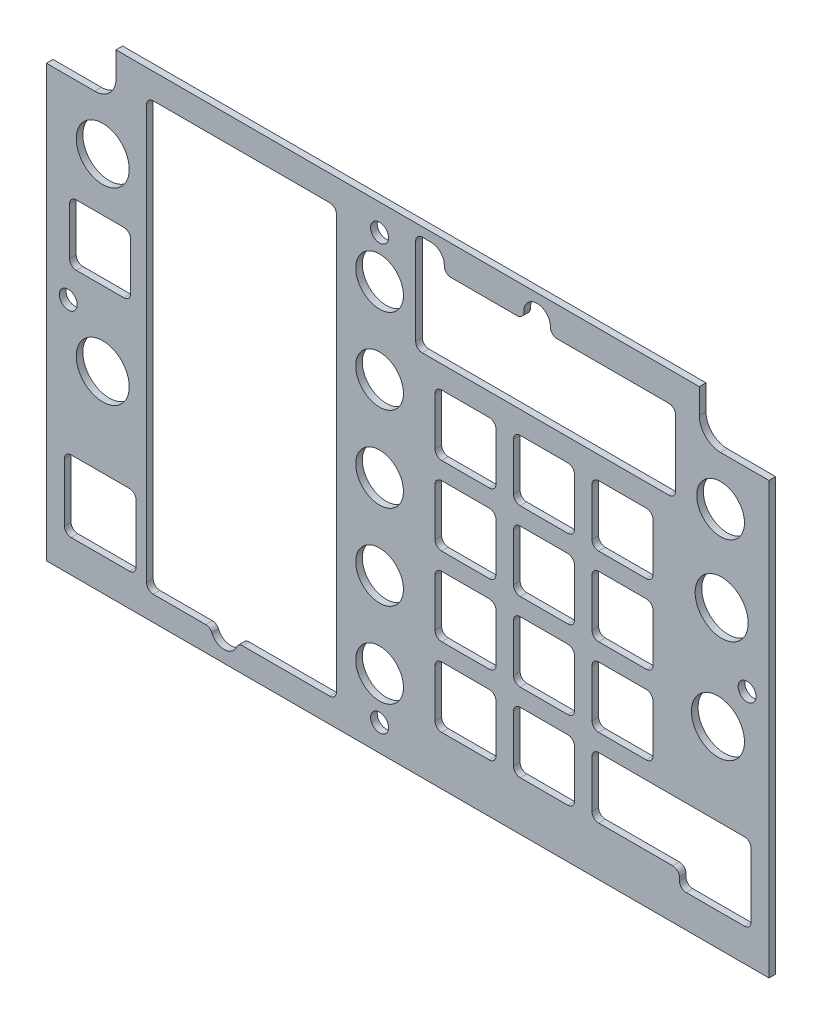
SolidWorks part; units mm, degrees
material "ABS PC"
ref_plane "Front Plane" through (0, 0, 0) normal (0, 0, 1) x (1, 0, 0)
ref_plane "Top Plane" through (0, 0, 0) normal (0, 1, 0) x (1, 0, 0)
ref_plane "Right Plane" through (0, 0, 0) normal (1, 0, 0) x (0, 0, -1)
sketch "Sketch1" plane through (0, 0, 0) normal (0, 0, 1) x (1, 0, 0)
  line L8 (58.2068, 169.534) -> (58.2068, 175.5665)
  line L9 (58.2068, 175.5665) -> (-81.4932, 175.5665)
  line L10 (-81.4932, 175.5665) -> (-81.4932, 169.534)
  line L11 (-86.5732, 164.454) -> (-98.162, 164.454)
  line L12 (-98.162, 164.454) -> (-98.162, 61.2665)
  line L13 (-98.162, 61.2665) -> (74.8755, 61.2665)
  line L14 (74.8755, 61.2665) -> (74.8755, 164.454)
  line L15 (74.8755, 164.454) -> (63.2868, 164.454)
  line L16 (58.2068, 169.534) -> (58.2068, 175.5665)
  line L17 (58.2068, 175.5665) -> (-81.4932, 175.5665)
  line L18 (-81.4932, 175.5665) -> (-81.4932, 169.534)
  line L19 (-86.5732, 164.454) -> (-98.162, 164.454)
  line L20 (-98.162, 164.454) -> (-98.162, 61.2665)
  line L21 (-98.162, 61.2665) -> (74.8755, 61.2665)
  line L22 (74.8755, 61.2665) -> (74.8755, 164.454)
  line L23 (74.8755, 164.454) -> (63.2868, 164.454)
  arc A2 (58.2068, 169.534) -> (63.2868, 164.454) centre (63.2868, 169.534) ccw
  arc A3 (-86.5732, 164.454) -> (-81.4932, 169.534) centre (-86.5732, 169.534) ccw
  arc A4 (58.2068, 169.534) -> (63.2868, 164.454) centre (63.2868, 169.534) ccw
  arc A5 (-86.5732, 164.454) -> (-81.4932, 169.534) centre (-86.5732, 169.534) ccw
  dimension "D1" = 0
extrude "Boss-Extrude1" add sketch "Sketch1" along normal blind 1.5875
sketch "Sketch2" plane through (0, 0, 1.5875) normal (0, 0, 1) x (1, 0, 0)
  line L0 (32.4893, 129.402) -> (47.0943, 129.402)
  line L1 (32.4893, 144.007) -> (32.4893, 129.402)
  line L2 (47.0943, 144.007) -> (32.4893, 144.007)
  line L3 (47.0943, 129.402) -> (47.0943, 144.007)
  line L4 (69.005, 84.6495) -> (55.005, 70.6495) construction
  line L5 (-78.2558, 84.633) -> (-92.2558, 70.633) construction
  line L6 (70.5775, 69.077) -> (53.4325, 69.077)
  line L7 (70.5775, 69.077) -> (70.5775, 86.222)
  line L8 (70.5775, 86.222) -> (53.4325, 86.222)
  line L9 (53.4325, 69.077) -> (53.4325, 86.222)
  line L10 (70.5775, 69.077) -> (53.4325, 86.222) construction
  line L11 (70.5775, 86.222) -> (53.4325, 69.077) construction
  line L12 (13.6933, 129.402) -> (28.2983, 129.402)
  line L13 (13.6933, 144.007) -> (13.6933, 129.402)
  line L14 (28.2983, 144.007) -> (13.6933, 144.007)
  line L15 (28.2983, 129.402) -> (28.2983, 144.007)
  line L16 (9.5023, 144.007) -> (-5.1027, 144.007)
  line L17 (9.5023, 129.402) -> (9.5023, 144.007)
  line L18 (-5.1027, 129.402) -> (9.5023, 129.402)
  line L19 (-5.1027, 144.007) -> (-5.1027, 129.402)
  line L20 (32.4893, 110.606) -> (32.4893, 129.402) construction
  line L22 (49.8768, 158.9295) -> (-7.1232, 158.9295) construction
  line L23 (52.4918, 168.4545) -> (-9.7382, 168.4545)
  line L24 (52.4918, 168.4545) -> (52.4918, 149.4045)
  line L25 (52.4918, 149.4045) -> (-9.7382, 149.4045)
  line L26 (32.4893, 73.014) -> (47.0943, 73.014)
  line L27 (32.4893, 87.619) -> (32.4893, 73.014)
  line L28 (47.0943, 87.619) -> (32.4893, 87.619)
  line L29 (47.0943, 73.014) -> (47.0943, 87.619)
  line L30 (32.4893, 73.014) -> (47.0943, 73.014)
  line L31 (32.4893, 87.619) -> (32.4893, 73.014)
  line L32 (47.0943, 87.619) -> (32.4893, 87.619)
  line L33 (47.0943, 73.014) -> (47.0943, 87.619)
  line L34 (32.4893, 91.81) -> (47.0943, 91.81)
  line L35 (32.4893, 106.415) -> (32.4893, 91.81)
  line L36 (47.0943, 106.415) -> (32.4893, 106.415)
  line L37 (47.0943, 91.81) -> (47.0943, 106.415)
  line L38 (32.4893, 91.81) -> (47.0943, 91.81)
  line L39 (32.4893, 106.415) -> (32.4893, 91.81)
  line L40 (47.0943, 106.415) -> (32.4893, 106.415)
  line L41 (47.0943, 91.81) -> (47.0943, 106.415)
  line L42 (32.4893, 110.606) -> (47.0943, 110.606)
  line L43 (32.4893, 125.211) -> (32.4893, 110.606)
  line L44 (47.0943, 125.211) -> (32.4893, 125.211)
  line L45 (47.0943, 110.606) -> (47.0943, 125.211)
  line L46 (32.4893, 110.606) -> (47.0943, 110.606)
  line L47 (32.4893, 125.211) -> (32.4893, 110.606)
  line L48 (47.0943, 125.211) -> (32.4893, 125.211)
  line L49 (47.0943, 110.606) -> (47.0943, 125.211)
  line L50 (-9.7382, 168.4545) -> (-9.7382, 149.4045)
  line L51 (13.6933, 73.014) -> (28.2983, 73.014)
  line L52 (13.6933, 87.619) -> (13.6933, 73.014)
  line L53 (28.2983, 87.619) -> (13.6933, 87.619)
  line L54 (28.2983, 73.014) -> (28.2983, 87.619)
  line L55 (13.6933, 73.014) -> (28.2983, 73.014)
  line L56 (13.6933, 87.619) -> (13.6933, 73.014)
  line L57 (28.2983, 87.619) -> (13.6933, 87.619)
  line L58 (28.2983, 73.014) -> (28.2983, 87.619)
  line L59 (13.6933, 91.81) -> (28.2983, 91.81)
  line L60 (13.6933, 106.415) -> (13.6933, 91.81)
  line L61 (28.2983, 106.415) -> (13.6933, 106.415)
  line L62 (-93.8283, 69.0605) -> (-76.6833, 69.0605)
  line L63 (-93.8283, 69.0605) -> (-93.8283, 86.2055)
  line L64 (-93.8283, 86.2055) -> (-76.6833, 86.2055)
  line L65 (-76.6833, 69.0605) -> (-76.6833, 86.2055)
  line L66 (-93.8283, 69.0605) -> (-76.6833, 86.2055) construction
  line L67 (-93.8283, 86.2055) -> (-76.6833, 69.0605) construction
  line L94 (28.2983, 91.81) -> (28.2983, 106.415)
  line L95 (13.6933, 91.81) -> (28.2983, 91.81)
  line L96 (13.6933, 106.415) -> (13.6933, 91.81)
  line L97 (28.2983, 106.415) -> (13.6933, 106.415)
  line L98 (28.2983, 91.81) -> (28.2983, 106.415)
  line L99 (13.6933, 110.606) -> (28.2983, 110.606)
  line L100 (13.6933, 125.211) -> (13.6933, 110.606)
  line L101 (28.2983, 125.211) -> (13.6933, 125.211)
  line L102 (28.2983, 110.606) -> (28.2983, 125.211)
  line L103 (13.6933, 110.606) -> (28.2983, 110.606)
  line L104 (13.6933, 125.211) -> (13.6933, 110.606)
  line L105 (28.2983, 125.211) -> (13.6933, 125.211)
  line L106 (28.2983, 110.606) -> (28.2983, 125.211)
  line L107 (9.5023, 125.211) -> (-5.1027, 125.211)
  line L108 (9.5023, 110.606) -> (9.5023, 125.211)
  line L109 (-5.1027, 110.606) -> (9.5023, 110.606)
  line L110 (-5.1027, 125.211) -> (-5.1027, 110.606)
  line L111 (9.5023, 125.211) -> (-5.1027, 125.211)
  line L112 (9.5023, 110.606) -> (9.5023, 125.211)
  line L113 (-5.1027, 110.606) -> (9.5023, 110.606)
  line L114 (-5.1027, 125.211) -> (-5.1027, 110.606)
  line L115 (-5.1027, 91.81) -> (9.5023, 91.81)
  line L116 (-5.1027, 106.415) -> (-5.1027, 91.81)
  line L117 (9.5023, 106.415) -> (-5.1027, 106.415)
  line L118 (9.5023, 91.81) -> (9.5023, 106.415)
  line L119 (-5.1027, 91.81) -> (9.5023, 91.81)
  line L120 (-5.1027, 106.415) -> (-5.1027, 91.81)
  line L121 (9.5023, 106.415) -> (-5.1027, 106.415)
  line L122 (9.5023, 91.81) -> (9.5023, 106.415)
  line L123 (-5.1027, 73.014) -> (9.5023, 73.014)
  line L124 (-5.1027, 87.619) -> (-5.1027, 73.014)
  line L125 (9.5023, 87.619) -> (-5.1027, 87.619)
  line L126 (9.5023, 73.014) -> (9.5023, 87.619)
  line L127 (-5.1027, 73.014) -> (9.5023, 73.014)
  line L128 (-5.1027, 87.619) -> (-5.1027, 73.014)
  line L129 (9.5023, 87.619) -> (-5.1027, 87.619)
  line L130 (9.5023, 73.014) -> (9.5023, 87.619)
  line L131 (-78.0007, 139.689) -> (-92.6057, 139.689)
  line L132 (-78.0007, 125.084) -> (-78.0007, 139.689)
  line L133 (-92.6057, 125.084) -> (-78.0007, 125.084)
  line L134 (-92.6057, 139.689) -> (-92.6057, 125.084)
  line L135 (-78.0007, 139.689) -> (-92.6057, 139.689)
  line L136 (-78.0007, 125.084) -> (-78.0007, 139.689)
  line L137 (-92.6057, 125.084) -> (-78.0007, 125.084)
  line L138 (-92.6057, 139.689) -> (-92.6057, 125.084)
  line L139 (-74.1732, 67.1295) -> (-28.7112, 67.1295)
  line L140 (-74.1732, 169.4495) -> (-74.1732, 67.1295)
  line L141 (-28.7112, 169.4495) -> (-74.1732, 169.4495)
  line L142 (-28.7112, 67.1295) -> (-28.7112, 169.4495)
  line L143 (-74.1732, 67.1295) -> (-28.7112, 67.1295)
  line L144 (-74.1732, 169.4495) -> (-74.1732, 67.1295)
  line L145 (-28.7112, 169.4495) -> (-74.1732, 169.4495)
  line L146 (-28.7112, 67.1295) -> (-28.7112, 169.4495)
  circle A0 centre (-84.6682, 152.389) radius 6.35
  circle A1 centre (-84.6682, 107.304) radius 6.35
  circle A2 centre (63.5408, 132.3865) radius 6.35
  circle A3 centre (62.6518, 107.304) radius 6.35
  circle A10 centre (-18.3742, 77.7765) radius 5.715 construction
  circle A11 centre (-18.3742, 98.0965) radius 5.715 construction
  circle A12 centre (-18.3742, 118.4165) radius 5.715 construction
  circle A13 centre (-18.3742, 138.7365) radius 5.715 construction
  circle A14 centre (-18.3742, 159.0565) radius 5.715 construction
  circle A15 centre (-18.3742, 77.7765) radius 5.715
  circle A16 centre (-18.3742, 98.0965) radius 5.715
  circle A17 centre (-18.3742, 118.4165) radius 5.715
  circle A18 centre (-18.3742, 138.7365) radius 5.715
  circle A19 centre (-18.3742, 159.0565) radius 5.715
  circle A20 centre (63.2868, 152.7065) radius 5.715 construction
  circle A21 centre (63.2868, 152.7065) radius 5.715
  point P94 (-85.2558, 77.633)
  point P97 (-85.2558, 77.633)
  point P98 (62.005, 77.6495)
  point P99 (62.005, 77.6495)
  point P104 (21.3768, 158.9295)
  point P109 (21.3768, 168.4545)
  point P113 (52.4918, 158.9295)
  dimension "D1" = 12.7
  dimension "D16" = 18.796
  dimension "D17" = 19.05
  dimension "D18" = 62.23
  dimension "D2" = 17.145
  dimension "D3" = 0
  dimension "D4" = 0
  dimension "D5" = 0
  dimension "D6" = 2
  dimension "D7" = 0
  dimension "D8" = 0
  dimension "D9" = 0
  dimension "D10" = 0
  dimension "D11" = 0
  dimension "D12" = 0
  dimension "D13" = 0
  dimension "D14" = 0
extrude "Cut-Extrude1" cut sketch "Sketch2" against normal through all
hole_wizard "#6 Clearance Hole2" positions "Sketch5" profile "Sketch6" hole size "#6" standard "ANSI Inch" end condition through all
sketch "Sketch5" plane through (-11.6432, -6.6627, -3.175) normal (0, 0, -1) x (-1, 0, 0)
  point P0 (-81.28, 124.6982)
  point P3 (6.731, 175.8792)
  point P6 (81.28, 124.6982)
  point P9 (6.731, 74.2792)
sketch "Sketch6" plane through (69.6368, 118.0355, -3.175) normal (1, 0, 0) x (0, 1, 0)
  line L0 (0, 0) -> (0, 4.7625)
  line L1 (0, 4.7625) -> (2.1526, 4.7625)
  line L2 (2.1526, 4.7625) -> (2.1526, 0)
  line L3 (2.1526, 0) -> (0, 0)
  line L4 (0, -6.35) -> (0, 107.95) construction
  dimension "Thru Hole Dia." = 4.3053
  dimension "Thru Hole Depth" = 4.7625
sketch "Sketch7" plane through (0, 0, 1.5875) normal (0, 0, 1) x (1, 0, 0)
  line L0 (62.005, 85.1738) -> (62.005, 70.1738) construction
  line L1 (54.505, 85.1738) -> (69.505, 85.1738)
  line L2 (54.505, 85.1738) -> (54.505, 70.1738)
  line L3 (54.505, 70.1738) -> (69.505, 70.1738)
  line L4 (69.505, 85.1738) -> (69.505, 70.1738)
  line L5 (-77.7558, 70.1165) -> (-92.7558, 70.1165)
  line L6 (-77.7558, 70.1165) -> (-77.7558, 85.1165)
  line L7 (-77.7558, 85.1165) -> (-92.7558, 85.1165)
  line L8 (-92.7558, 70.1165) -> (-92.7558, 85.1165)
  line L9 (-85.2558, 85.1165) -> (-85.2558, 70.1165) construction
  point P10 (62.005, 77.6738)
  point P13 (-85.2558, 77.6165)
  dimension "D1" = 15
extrude "Cut-Extrude2" [suppressed] cut sketch "Sketch7" against normal up to next
hole_wizard "1/4 (0.25) Diameter Hole1" positions "Sketch8" profile "Sketch9" hole size "1/4" standard "ANSI Inch" end condition through all
sketch "Sketch8" plane through (0, 0, 0) normal (0, 0, -1) x (-1, 0, 0)
  point P0 (55.5832, 67.3415)
  point P2 (-49.8268, 81.9465)
  point P4 (-19.3468, 170.2115)
  point P6 (6.0532, 170.2115)
sketch "Sketch9" plane through (-55.5832, 67.3415, 0) normal (1, 0, 0) x (0, 1, 0)
  line L0 (0, 0) -> (0, 1.5875)
  line L1 (0, 1.5875) -> (3.175, 1.5875)
  line L2 (3.175, 1.5875) -> (3.175, 0)
  line L5 (3.175, 0) -> (0, 0)
  line L11 (0, -6.35) -> (0, 107.95) construction
  dimension "Thru Hole Dia." = 6.35
  dimension "Thru Hole Depth" = 1.5875
sketch "Sketch10" plane through (0, 0, 0) normal (0, 0, -1) x (-1, 0, 0)
  line L0 (9.7382, 168.4545) -> (9.7382, 173.3865)
  line L1 (9.7382, 168.4545) -> (9.7382, 149.4045) construction
  line L2 (9.7382, 168.4545) -> (8.6978, 168.4545)
  line L3 (6.0532, 173.3865) -> (9.7382, 173.3865)
  line L4 (-47.0943, 87.619) -> (-32.4893, 87.619) construction
  line L6 (-47.0943, 87.619) -> (-47.0943, 73.014)
  line L7 (-47.0943, 73.014) -> (-53.4325, 73.014)
  line L8 (-53.4325, 86.222) -> (-53.4325, 73.014)
  line L9 (-47.0943, 83.5633) -> (-47.0943, 87.619) construction
  line L10 (-53.4325, 86.222) -> (-53.4325, 69.077) construction
  line L11 (-32.4893, 73.014) -> (-47.0943, 73.014) construction
  line L12 (-70.5775, 86.222) -> (-53.4325, 86.222) construction
  line L13 (-47.0943, 87.619) -> (-70.5775, 87.619)
  line L15 (-53.4325, 86.222) -> (-70.5775, 86.222)
  line L16 (-70.5775, 87.619) -> (-70.5775, 86.222)
  line L17 (-70.5775, 69.077) -> (-70.5775, 86.222) construction
  arc A0 (8.6978, 168.4545) -> (3.4087, 168.4545) centre (6.0532, 170.2115) ccw construction
  arc A1 (8.6978, 168.4545) -> (6.0532, 173.3865) centre (6.0532, 170.2115) ccw
  point P25 (-47.6309, 87.619)
extrude "Cut-Extrude3" cut sketch "Sketch10" against normal through all
fillet "Fillet1" radius 1.5875 70 edges at (-78.0007, 139.689, 0.7937) (-78.0007, 125.084, 0.7937) (-92.6057, 125.084, 0.7937) (-92.6057, 139.689, 0.7937) (-74.1732, 169.4495, 0.7937) (-28.7112, 169.4495, 0.7937) (-28.7112, 67.1295, 0.7937) (-52.4153, 67.1295, 0.7937) (-58.7512, 67.1295, 0.7937) (-74.1732, 67.1295, 0.7937) (-93.8283, 69.0605, 0.7937) (-93.8283, 86.2055, 0.7937) (-76.6833, 86.2055, 0.7937) (-76.6833, 69.0605, 0.7937) (32.4893, 73.014, 0.7937) (70.5775, 87.619, 0.7937) (70.5775, 69.077, 0.7937) (53.4325, 69.077, 0.7937) (32.4893, 87.619, 0.7937) (13.6933, 73.014, 0.7937) (28.2983, 87.619, 0.7937) (28.2983, 73.014, 0.7937) (13.6933, 87.619, 0.7937) (-5.1027, 73.014, 0.7937) (9.5023, 87.619, 0.7937) (9.5023, 73.014, 0.7937) (-5.1027, 87.619, 0.7937) (-5.1027, 91.81, 0.7937) (-5.1027, 106.415, 0.7937) (9.5023, 91.81, 0.7937) (9.5023, 106.415, 0.7937) (13.6933, 91.81, 0.7937) (13.6933, 106.415, 0.7937) (28.2983, 91.81, 0.7937) (28.2983, 106.415, 0.7937) (32.4893, 91.81, 0.7937) (47.0943, 106.415, 0.7937) (47.0943, 91.81, 0.7937) (32.4893, 106.415, 0.7937) (32.4893, 110.606, 0.7937) (47.0943, 125.211, 0.7937) (47.0943, 110.606, 0.7937) (32.4893, 125.211, 0.7937) (13.6933, 110.606, 0.7937) (28.2983, 125.211, 0.7937) (28.2983, 110.606, 0.7937) (13.6933, 125.211, 0.7937) (9.5023, 110.606, 0.7937) (-5.1027, 110.606, 0.7937) (-5.1027, 125.211, 0.7937) (9.5023, 125.211, 0.7937) (9.5023, 129.402, 0.7937) (-5.1027, 129.402, 0.7937) (-5.1027, 144.007, 0.7937) (9.5023, 144.007, 0.7937) (13.6933, 129.402, 0.7937) (13.6933, 144.007, 0.7937) (28.2983, 129.402, 0.7937) (28.2983, 144.007, 0.7937) (32.4893, 129.402, 0.7937) (47.0943, 144.007, 0.7937) (47.0943, 129.402, 0.7937) (32.4893, 144.007, 0.7937) (52.4918, 168.4545, 0.7937) (52.4918, 149.4045, 0.7937) (-9.7382, 149.4045, 0.7937) (-9.7382, 173.3865, 0.7937) (-3.4087, 168.4545, 0.7937) (16.7022, 168.4545, 0.7937) (21.9913, 168.4545, 0.7937)
fillet "Fillet2" radius 1.5875 1 edges at (53.4325, 73.014, 0.7937)
